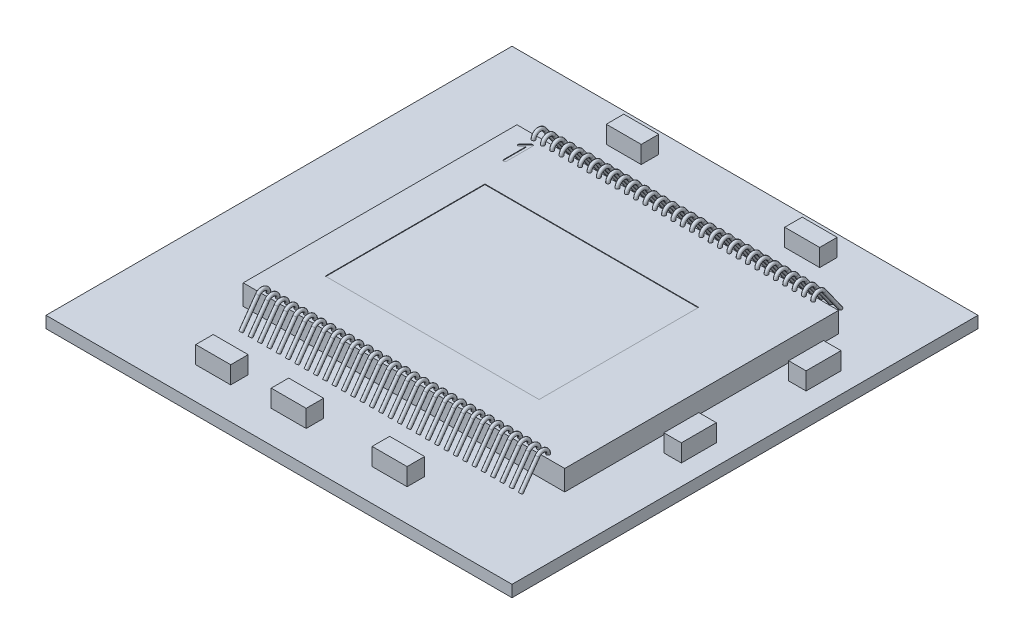
SolidWorks part; units mm, degrees
material "1060 Legierung"
ref_plane "Vorne" through (0, 0, 0) normal (0, 0, 1) x (1, 0, 0)
ref_plane "Oben" through (0, 0, 0) normal (0, 1, 0) x (1, 0, 0)
ref_plane "Rechts" through (0, 0, 0) normal (1, 0, 0) x (0, 0, -1)
ref_plane "Faser-Ebene_Vorne" through (0, 0, 0.175) normal (0, 0, 1) x (1, 0, 0)
ref_plane "Faser-Ebene_Rechts" through (-0.32, 0, 0) normal (1, 0, 0) x (0, 0, -1)
sketch "Skizze1" plane through (0, 0, 0) normal (0, 1, 0) x (1, 0, 0)
  line L0 (-2.76, 2.35) -> (2.76, -2.35) construction
  line L1 (-2.76, 2.35) -> (2.76, 2.35)
  line L2 (-2.76, 2.35) -> (-2.76, -2.35)
  line L3 (-2.76, -2.35) -> (2.76, -2.35)
  line L4 (2.76, 2.35) -> (2.76, -2.35)
  dimension "D1" = 5.52
  dimension "D2" = 4.7
extrude "Chip_Die" add sketch "Skizze1" along normal blind 0.35
sketch "Skizze4" plane through (0, 0.35, 0) normal (0, 1, 0) x (1, 0, 0)
  line L1 (-2.155, 1.195) -> (1.515, 1.195)
  line L2 (-2.155, 1.195) -> (-2.155, -1.545)
  line L3 (-2.155, -1.545) -> (1.515, -1.545)
  line L4 (1.515, 1.195) -> (1.515, -1.545)
  line L5 (-0.32, 1.195) -> (-0.32, -0.1113) construction
  line L7 (-0.32, -0.1925) -> (-0.32, 0.1925) construction
  line L8 (1.515, -0.175) -> (0.7734, -0.175) construction
  line L9 (-0.1925, -0.175) -> (0.1925, -0.175) construction
  dimension "D1" = 3.67
  dimension "D2" = 2.74
extrude "Active_Area" cut sketch "Skizze4" against normal blind 0.01
sketch "Skizze5" plane through (0, 0.35, 0) normal (0, 1, 0) x (1, 0, 0)
  text T0 "1" font "ISOCPEUR" height 0.5
extrude "Pin1" cut sketch "Skizze5" against normal blind 0.01
sketch "Skizze6" plane through (0, 0, 0) normal (0, 1, 0) x (1, 0, 0)
  line L0 (-2.155, 1.195) -> (1.515, -1.545) construction
  line L1 (-4.32, 3.825) -> (3.68, 3.825)
  line L2 (-4.32, 3.825) -> (-4.32, -4.175)
  line L3 (-4.32, -4.175) -> (3.68, -4.175)
  line L4 (3.68, 3.825) -> (3.68, -4.175)
  line L5 (3.68, 3.825) -> (-4.32, -4.175) construction
  point P7 (-0.32, -0.175)
  dimension "D1" = 8
extrude "Base-Plate" add sketch "Skizze6" against normal blind 0.2
sketch "Skizze12" plane through (0, 0, 0) normal (1, 0, 0) x (0, 0, -1)
  line L0 (-2.35, 0.35) -> (2.35, 0.35) construction
  line L1 (-2.4563, 0.4079) -> (-2.7458, 0)
  line L2 (-4.175, 0) -> (3.825, 0) construction
  line L3 (0, 0) -> (0, 1.1196) construction
  arc A0 (-2.2748, 0.35) -> (-2.4563, 0.4079) centre (-2.3748, 0.35) ccw
  dimension "D1" = 0.1
sketch "Skizze13" plane through (0, 0.35, 0) normal (0, 1, 0) x (1, 0, 0)
  line L0 (0, 0) -> (0, -1.1473) construction
  circle A0 centre (0, -2.2748) radius 0.03
  circle A1 centre (0.16, -2.2748) radius 0.03
  circle A2 centre (0.32, -2.2748) radius 0.03
  circle A3 centre (0.48, -2.2748) radius 0.03
  circle A4 centre (0.64, -2.2748) radius 0.03
  circle A5 centre (0.8, -2.2748) radius 0.03
  circle A6 centre (0.96, -2.2748) radius 0.03
  circle A7 centre (1.12, -2.2748) radius 0.03
  circle A8 centre (1.28, -2.2748) radius 0.03
  circle A9 centre (1.44, -2.2748) radius 0.03
  circle A10 centre (1.6, -2.2748) radius 0.03
  circle A11 centre (1.76, -2.2748) radius 0.03
  circle A12 centre (1.92, -2.2748) radius 0.03
  circle A13 centre (2.08, -2.2748) radius 0.03
  circle A14 centre (2.24, -2.2748) radius 0.03
  circle A15 centre (2.4, -2.2748) radius 0.03
  circle A16 centre (-2.4, -2.2748) radius 0.03
  circle A17 centre (-2.24, -2.2748) radius 0.03
  circle A18 centre (-2.08, -2.2748) radius 0.03
  circle A19 centre (-1.92, -2.2748) radius 0.03
  circle A20 centre (-1.76, -2.2748) radius 0.03
  circle A21 centre (-1.6, -2.2748) radius 0.03
  circle A22 centre (-1.44, -2.2748) radius 0.03
  circle A23 centre (-1.28, -2.2748) radius 0.03
  circle A24 centre (-1.12, -2.2748) radius 0.03
  circle A25 centre (-0.96, -2.2748) radius 0.03
  circle A26 centre (-0.8, -2.2748) radius 0.03
  circle A27 centre (-0.64, -2.2748) radius 0.03
  circle A28 centre (-0.48, -2.2748) radius 0.03
  circle A29 centre (-0.32, -2.2748) radius 0.03
  circle A30 centre (-0.16, -2.2748) radius 0.03
  dimension "D1" = 0.06
  dimension "D2" = 16
sweep "Bonding-wires" add profiles "Skizze13" path "Skizze12"
mirror "Spiegeln1" about plane through (0, 0, 0) normal (0, 0, 1) of "Bonding-wires"
sketch "Skizze14" plane through (0, 0, 0) normal (0, 1, 0) x (1, 0, 0)
  line L0 (-4.32, -4.175) -> (3.68, -4.175) construction
  line L1 (-2.2994, -3.325) -> (-1.6994, -3.325)
  line L2 (-2.2994, -3.325) -> (-2.2994, -3.625)
  line L3 (-2.2994, -3.625) -> (-1.6994, -3.625)
  line L4 (-1.6994, -3.325) -> (-1.6994, -3.625)
  line L5 (3.68, -4.175) -> (3.68, 3.825) construction
  line L6 (-1.0036, -3.325) -> (-0.4036, -3.325)
  line L7 (-1.0036, -3.325) -> (-1.0036, -3.625)
  line L8 (-1.0036, -3.625) -> (-0.4036, -3.625)
  line L9 (-0.4036, -3.325) -> (-0.4036, -3.625)
  line L10 (0.7291, -3.625) -> (1.3291, -3.625)
  line L11 (0.7291, -3.625) -> (0.7291, -3.325)
  line L12 (0.7291, -3.325) -> (1.3291, -3.325)
  line L13 (1.3291, -3.625) -> (1.3291, -3.325)
  line L14 (3.03, -0.3181) -> (3.33, -0.3181)
  line L15 (3.03, -0.3181) -> (3.03, -0.9181)
  line L16 (3.03, -0.9181) -> (3.33, -0.9181)
  line L17 (3.33, -0.3181) -> (3.33, -0.9181)
  line L18 (3.68, 3.825) -> (-4.32, 3.825) construction
  line L19 (3.03, 1.2236) -> (3.33, 1.2236)
  line L20 (3.03, 1.2236) -> (3.03, 1.8236)
  line L21 (3.03, 1.8236) -> (3.33, 1.8236)
  line L22 (3.33, 1.2236) -> (3.33, 1.8236)
  line L23 (-1.4515, 3.175) -> (-2.0515, 3.175)
  line L24 (-1.4515, 3.175) -> (-1.4515, 3.475)
  line L25 (-1.4515, 3.475) -> (-2.0515, 3.475)
  line L26 (-2.0515, 3.175) -> (-2.0515, 3.475)
  line L28 (1.012, 3.475) -> (1.612, 3.475)
  line L29 (1.012, 3.475) -> (1.012, 3.175)
  line L30 (1.012, 3.175) -> (1.612, 3.175)
  line L31 (1.612, 3.475) -> (1.612, 3.175)
  dimension "D1" = 0.3
  dimension "D2" = 0.6
  dimension "D3" = 0.55
  dimension "D4" = 0.35
  dimension "D5" = 0.35
extrude "Electronic_components" add sketch "Skizze14" along normal blind 0.3
